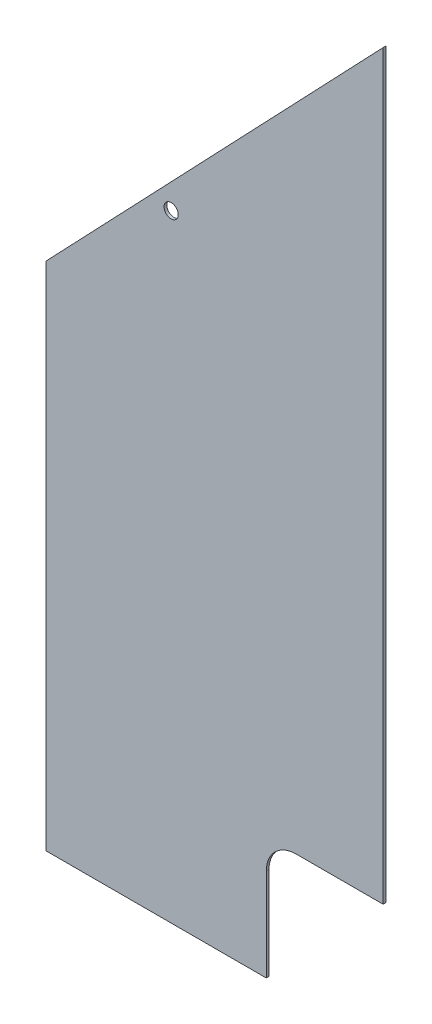
SolidWorks part; units mm, degrees
material "PC High Viscosity"
ref_plane "Front Plane" through (0, 0, 0) normal (0, 0, 1) x (1, 0, 0)
ref_plane "Top Plane" through (0, 0, 0) normal (0, 1, 0) x (1, 0, 0)
ref_plane "Right Plane" through (0, 0, 0) normal (1, 0, 0) x (0, 0, -1)
sketch "Sketch1" plane through (0, 0, 0) normal (0, 0, 1) x (1, 0, 0)
  line L0 (0, 0) -> (-393.7, 0)
  line L1 (-393.7, 0) -> (-393.7, 596.9)
  line L2 (-393.7, 596.9) -> (0, 1009.65)
  line L4 (0, 1009.65) -> (0, 0)
  dimension "D1" = 596.9
  dimension "D2" = 393.7
  dimension "D3" = 1009.65
extrude "Boss-Extrude1" add sketch "Sketch1" along normal blind 3.175
sketch "Sketch2" plane through (0, 0, 3.175) normal (0, 0, 1) x (1, 0, 0)
  line L0 (-393.7, 0) -> (0, 0) construction
  line L1 (-114.3, 101.6) -> (-88.9, 101.6)
  line L2 (-114.3, 101.6) -> (-114.3, 0)
  line L3 (-114.3, 0) -> (-88.9, 0)
  line L4 (-88.9, 101.6) -> (-88.9, 0)
  line L5 (-114.3, 101.6) -> (-88.9, 0) construction
  line L6 (-114.3, 0) -> (-88.9, 101.6) construction
  line L8 (-101.6, 101.6) -> (-101.6, 0) construction
  line L9 (-393.7, 596.9) -> (-393.7, 0) construction
  point P0 (-101.6, 50.8)
  dimension "D1" = 25.4
  dimension "D2" = 292.1
  dimension "D3" = 101.6
extrude "Cut-Extrude1" [suppressed] cut sketch "Sketch2" against normal through all
fillet "Fillet1" [suppressed] radius 12.7
sketch "Sketch4" plane through (0, 0, 3.175) normal (0, 0, 1) x (1, 0, 0)
  line L2 (-371.475, 579.7602) -> (-371.475, 620.2004)
  line L3 (-393.7, 66.675) -> (-381, 66.675)
  line L4 (-374.65, 73.025) -> (-374.65, 79.375)
  line L5 (-381, 85.725) -> (-393.7, 85.725)
  line L6 (-393.7, 85.725) -> (-393.7, 66.675)
  line L7 (-393.7, 0) -> (0, 0) construction
  line L8 (-393.7, 596.9) -> (-393.7, 0) construction
  line L9 (-393.7, 567.0602) -> (-384.175, 567.0602)
  line L10 (-371.475, 620.2004) -> (-393.7, 596.9)
  line L12 (-393.7, 596.9) -> (-393.7, 567.0602)
  line L13 (0, 1009.65) -> (-393.7, 596.9) construction
  arc A1 (-384.175, 567.0602) -> (-371.475, 579.7602) centre (-384.175, 579.7602) ccw
  arc A2 (-381, 66.675) -> (-374.65, 73.025) centre (-381, 73.025) ccw
  arc A3 (-374.65, 79.375) -> (-381, 85.725) centre (-381, 79.375) ccw
  point P20 (-393.7, 581.9801)
  dimension "D4" = 6.35
  dimension "D8" = 12.7
  dimension "D1" = 19.05
  dimension "D2" = 12.7
  dimension "D3" = 66.675
  dimension "D9" = 22.225
  dimension "D10" = 29.8398
sketch "Sketch3" [suppressed] plane through (0, 0, 0) normal (0, 0, 1) x (1, 0, 0)
  line L0 (0, 1009.65) -> (-395.2875, 622.3)
  line L1 (0, 0) -> (-1219.2, 0)
  line L2 (0, 0) -> (0, 2438.4)
  line L3 (0, 2438.4) -> (-1219.2, 2438.4)
  line L4 (-1219.2, 0) -> (-1219.2, 2438.4)
  line L5 (0, 1009.65) -> (-395.2875, 622.3) construction
  line L6 (-395.2875, 622.3) -> (-395.2875, 1612.9)
  line L7 (-395.2875, 1612.9) -> (0, 1612.9)
  line L8 (0, 1612.9) -> (0, 1009.65)
  line L9 (-395.2875, 622.3) -> (-395.2875, 0) construction
  line L11 (-401.6375, 1612.9) -> (-796.925, 1612.9)
  line L12 (-401.6375, 1612.9) -> (-401.6375, 0)
  line L13 (-401.6375, 0) -> (-796.925, 0)
  line L14 (-796.925, 1612.9) -> (-796.925, 0)
  line L15 (-823.9125, 1612.9) -> (-1219.2, 1612.9)
  line L16 (-823.9125, 1612.9) -> (-823.9125, 0)
  line L17 (-823.9125, 0) -> (-1219.2, 0)
  line L18 (-1219.2, 1612.9) -> (-1219.2, 0)
  line L19 (0, 1641.0222) -> (-990.6, 1641.0222)
  line L20 (0, 1641.0222) -> (0, 2031.6742)
  line L21 (0, 2031.6742) -> (-990.6, 2031.6742)
  line L22 (-990.6, 1641.0222) -> (-990.6, 2031.6742)
  line L23 (0, 2047.748) -> (-991.848, 2047.748)
  line L24 (0, 2047.748) -> (0, 2438.4)
  line L25 (0, 2438.4) -> (-991.848, 2438.4)
  line L26 (-991.848, 2047.748) -> (-991.848, 2438.4)
  dimension "D1" = 1219.2
  dimension "D2" = 2438.4
  dimension "D3" = 990.6
  dimension "D4" = 6.35
  dimension "D5" = 990.6
  dimension "D6" = 390.652
extrude "Cut-Extrude2" [suppressed] cut sketch "Sketch4" against normal through all
sketch "Sketch5" plane through (0, 0, 3.175) normal (0, 0, 1) x (1, 0, 0)
  line L0 (-393.7, 0) -> (0, 0) construction
  line L2 (0, 0) -> (0, 1009.65) construction
  circle A1 centre (-247.65, 720.725) radius 8.255
  point P5 (0, 634.6059)
  dimension "D1" = 16.51
  dimension "D2" = 720.725
  dimension "D3" = 247.65
extrude "Cut-Extrude3" cut sketch "Sketch5" against normal through all
sketch "Sketch6" plane through (0, 0, 3.175) normal (0, 0, 1) x (1, 0, 0)
  line L6 (0, 0) -> (0, 1009.65) construction
  line L9 (0, 142.875) -> (-101.6, 142.875)
  line L10 (-136.525, 107.95) -> (-136.525, 0)
  line L11 (-393.7, 0) -> (0, 0) construction
  line L12 (0, 142.875) -> (0, 0)
  line L13 (0, 0) -> (-136.525, 0)
  arc A0 (-101.6, 142.875) -> (-136.525, 107.95) centre (-101.6, 107.95) ccw
  dimension "D1" = 34.925
  dimension "D2" = 136.525
  dimension "D3" = 142.875
extrude "Cut-Extrude4" cut sketch "Sketch6" against normal through all
